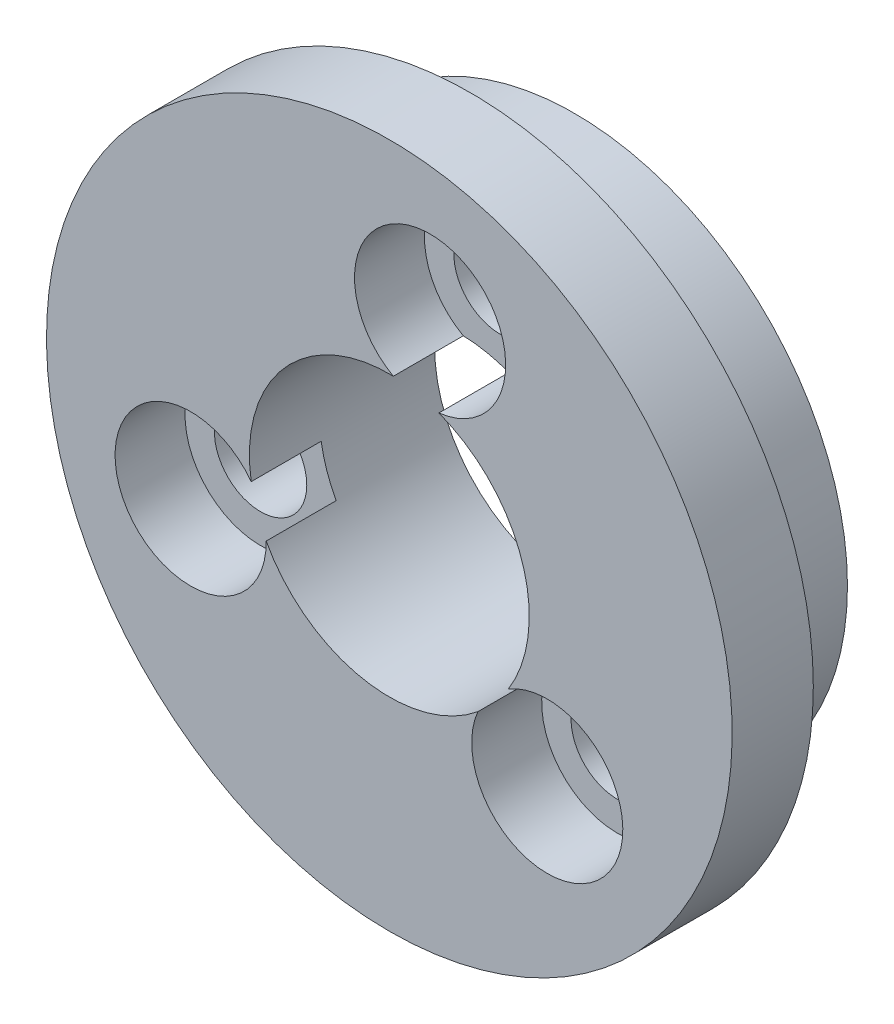
SolidWorks part; units mm, degrees
ref_plane "Front Plane" through (0, 0, 0) normal (0, 0, 1) x (1, 0, 0)
ref_plane "Top Plane" through (0, 0, 0) normal (0, 1, 0) x (1, 0, 0)
ref_plane "Right Plane" through (0, 0, 0) normal (1, 0, 0) x (0, 0, -1)
sketch "Sketch1" plane through (0, 0, 0) normal (0, 0, 1) x (1, 0, 0)
  circle A0 centre (350.15, -0.3675) radius 12.25
  dimension "D1" = 24.5
extrude "Boss-Extrude1" add sketch "Sketch1" along normal up to surface (2.9 mm away)
sketch "Sketch2" plane through (0, 0, 2.9) normal (0, 0, 1) x (1, 0, 0)
  circle A0 centre (350.15, -0.3675) radius 5
  dimension "D1" = 10
extrude "Cut-Extrude1" cut sketch "Sketch2" against normal up to next
sketch "Sketch5" plane through (0, 0, 2.9) normal (0, 0, 1) x (1, 0, 0)
  line L0 (340.6836, -3.5905) -> (352.092, 9.4421) construction
  line L1 (352.092, 9.4421) -> (357.6744, -6.9542) construction
  line L2 (357.6744, -6.9542) -> (340.6836, -3.5905) construction
  line L3 (350.15, -0.3675) -> (355.7933, -5.3075) construction
  line L6 (350.15, -0.3675) -> (343.0502, -2.7847) construction
  line L7 (350.15, -0.3675) -> (351.6065, 6.9897) construction
  circle A1 centre (350.15, -0.3675) radius 5 construction
  circle A3 centre (343.0502, -2.7847) radius 1.65
  circle A4 centre (355.7933, -5.3075) radius 1.65
  circle A5 centre (351.6065, 6.9897) radius 1.65
  dimension "D2" = 3.3
  dimension "D1" = 7.5
extrude "Cut-Extrude2" cut sketch "Sketch5" against normal up to next
sketch "Sketch6" plane through (0, 0, 0) normal (0, 0, -1) x (-1, 0, 0)
  circle A0 centre (-350.15, -0.3675) radius 9.75
  circle A3 centre (-350.15, -0.3675) radius 5
  dimension "D1" = 19.5
extrude "Boss-Extrude2" add sketch "Sketch6" along normal up to surface (3.72 mm away)
sketch "Sketch7" plane through (0, 0, 0) normal (0, 0, 1) x (1, 0, 0)
  circle A0 centre (351.6065, 6.9897) radius 1.65
  circle A1 centre (343.0502, -2.7847) radius 1.65
  circle A2 centre (355.7933, -5.3075) radius 1.65
extrude "Cut-Extrude3" cut sketch "Sketch7" against normal up to surface (3.72 mm away) up to face at (350.15, -5.3675, -3.72)
sketch "Sketch8" plane through (0, 0, 2.9) normal (0, 0, 1) x (1, 0, 0)
  circle A0 centre (351.6065, 6.9897) radius 2.7
  circle A1 centre (355.7933, -5.3075) radius 2.7
  circle A2 centre (343.0502, -2.7847) radius 2.7
  dimension "D1" = 5.4
extrude "Cut-Extrude4" cut sketch "Sketch8" against normal blind 2.5
